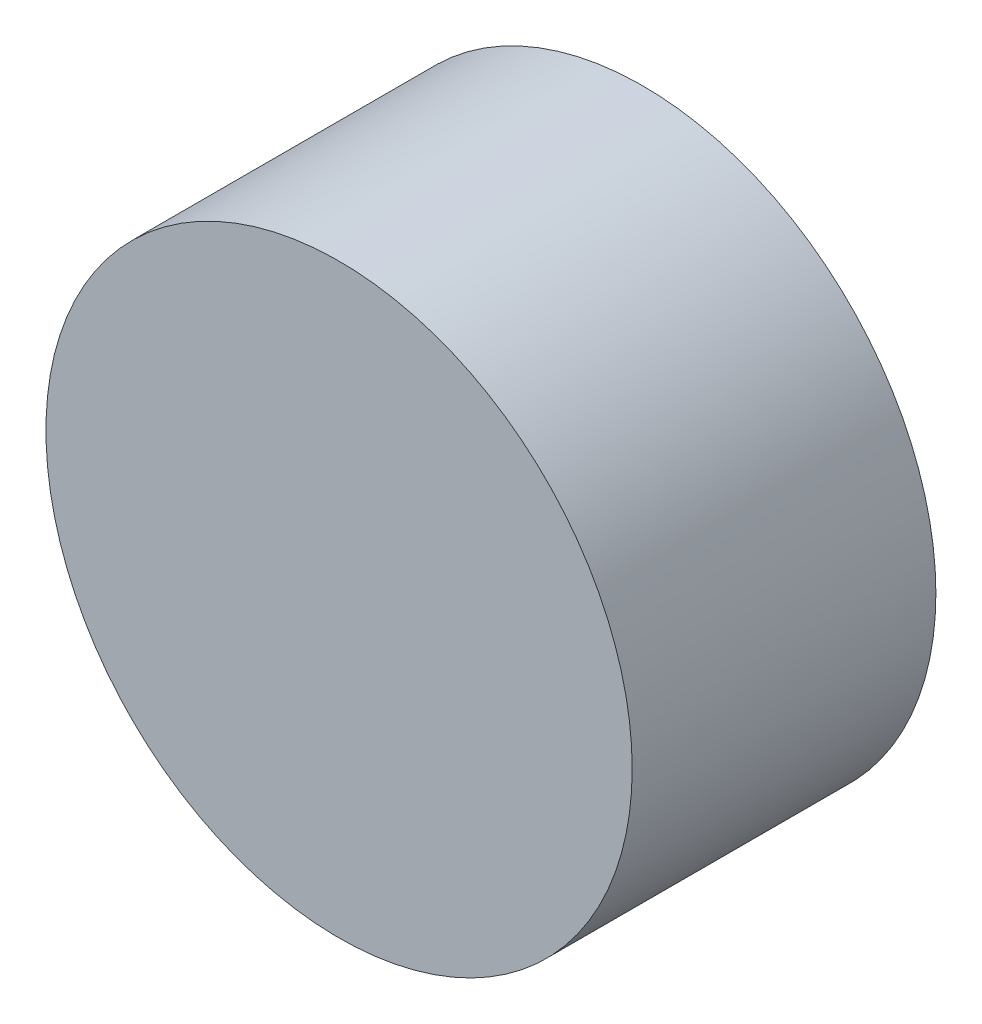
SolidWorks part; units mm, degrees
ref_plane "Front Plane" through (0, 0, 0) normal (0, 0, 1) x (1, 0, 0)
ref_plane "Top Plane" through (0, 0, 0) normal (0, 1, 0) x (1, 0, 0)
ref_plane "Right Plane" through (0, 0, 0) normal (1, 0, 0) x (0, 0, -1)
sketch "Sketch1" plane through (0, 0, 0) normal (0, 0, 1) x (1, 0, 0)
  circle A0 centre (0, 0) radius 4.826
  dimension "D1" = 9.652
extrude "Boss-Extrude1" add sketch "Sketch1" along normal blind 5
